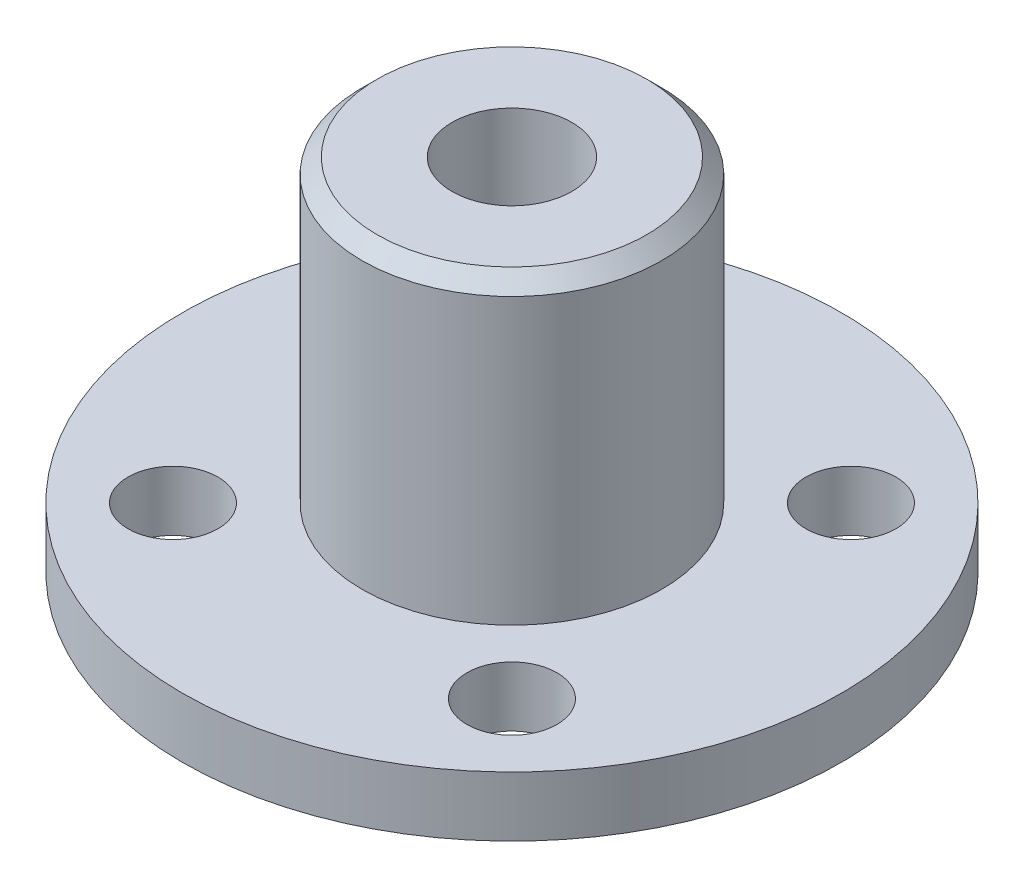
SolidWorks part; units mm, degrees
material "201 Annealed Stainless Steel (SS)"
ref_plane "Front Plane" through (0, 0, 0) normal (0, 0, 1) x (1, 0, 0)
ref_plane "Top Plane" through (0, 0, 0) normal (0, 1, 0) x (1, 0, 0)
ref_plane "Right Plane" through (0, 0, 0) normal (1, 0, 0) x (0, 0, -1)
sketch "Sketch1" plane through (0, 0, 0) normal (0, 1, 0) x (1, 0, 0)
  circle A0 centre (0, 0) radius 11
  dimension "D1" = 22
extrude "Boss-Extrude1" add sketch "Sketch1" along normal blind 2
sketch "Sketch2" plane through (0, 2, 0) normal (0, 1, 0) x (1, 0, 0)
  circle A0 centre (0, 0) radius 5
  dimension "D1" = 10
extrude "Boss-Extrude2" add sketch "Sketch2" along normal blind 10
sketch "Sketch3" plane through (0, 12, 0) normal (0, 1, 0) x (1, 0, 0)
  circle A0 centre (0, 0) radius 2
  dimension "D1" = 4
extrude "Cut-Extrude1" cut sketch "Sketch3" against normal through all
chamfer "Chamfer1" distance 0.5 angle 45 1 edges at (0, 12, 5)
sketch "Sketch4" plane through (0, 0, 0) normal (0, -1, 0) x (1, 0, 0)
  line L1 (-5.6569, 5.6569) -> (5.6569, 5.6569) construction
  line L2 (-5.6569, 5.6569) -> (-5.6569, -5.6569) construction
  line L3 (-5.6569, -5.6569) -> (5.6569, -5.6569) construction
  line L4 (5.6569, 5.6569) -> (5.6569, -5.6569) construction
  line L5 (-5.6569, 5.6569) -> (5.6569, -5.6569) construction
  line L6 (-5.6569, -5.6569) -> (5.6569, 5.6569) construction
  circle A0 centre (-5.6569, 5.6569) radius 1.5
  circle A1 centre (5.6569, 5.6569) radius 1.5
  circle A2 centre (5.6569, -5.6569) radius 1.5
  circle A3 centre (-5.6569, -5.6569) radius 1.5
  point P4 (0, 0)
  dimension "D1" = 3
  dimension "D2" = 16
extrude "Cut-Extrude2" cut sketch "Sketch4" against normal blind 10
